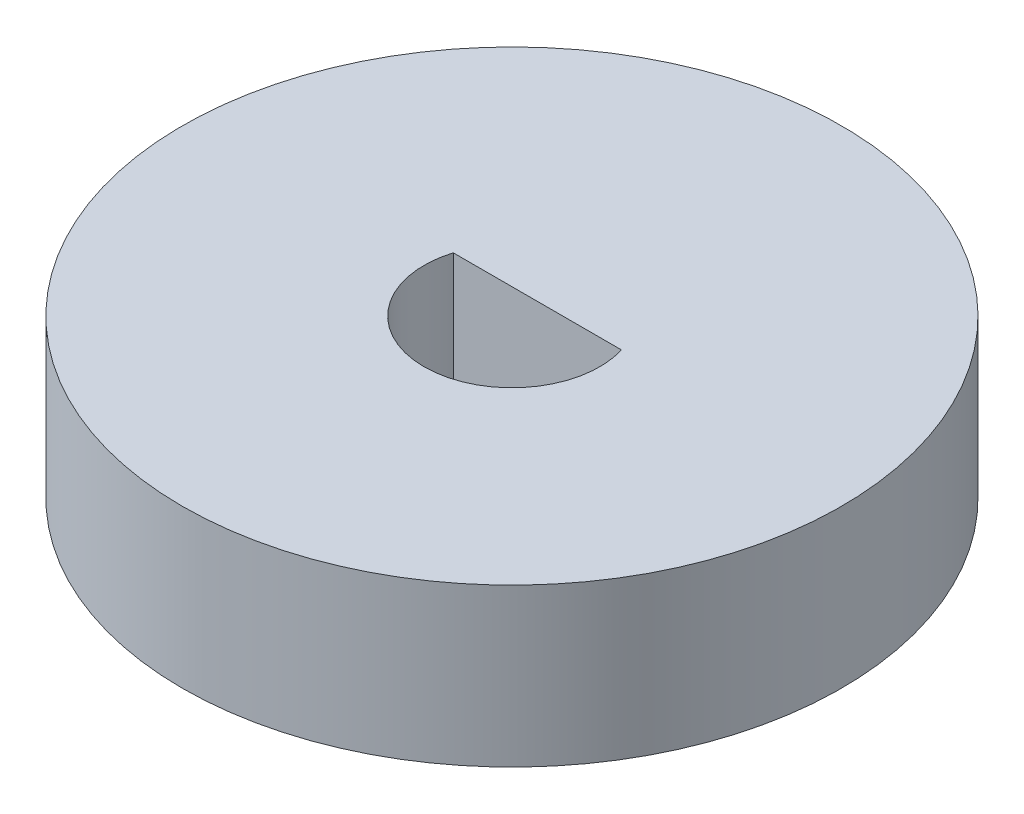
SolidWorks part; units mm, degrees
ref_plane "Front Plane" through (0, 0, 0) normal (0, 0, 1) x (1, 0, 0)
ref_plane "Top Plane" through (0, 0, 0) normal (0, 1, 0) x (1, 0, 0)
ref_plane "Right Plane" through (0, 0, 0) normal (1, 0, 0) x (0, 0, -1)
sketch "Sketch1" plane through (0, 0, 0) normal (0, 1, 0) x (1, 0, 0)
  circle A0 centre (0, 0) radius 11.25
  dimension "D1" = 22.5
extrude "Boss-Extrude1" add sketch "Sketch1" along normal blind 5.38
sketch "Sketch2" plane through (0, 5.38, 0) normal (0, 1, 0) x (1, 0, 0)
  circle A0 centre (0, 0) radius 3
  dimension "D1" = 6
extrude "Cut-Extrude1" cut sketch "Sketch2" against normal blind 5.38
sketch "Sketch3" plane through (0, 5.38, 0) normal (0, 1, 0) x (1, 0, 0)
  line L1 (-3, 3) -> (2.8715, 3)
  line L2 (-3, 3) -> (-3, 0.8685)
  line L3 (-3, 0.8685) -> (2.8715, 0.8685)
  line L4 (2.8715, 3) -> (2.8715, 0.8685)
  circle A0 centre (0, 0) radius 3 construction
extrude "Boss-Extrude2" add sketch "Sketch3" against normal blind 5.38
equation "\"AcrThickness\"= 5.38mm"
equation "\"D1@Boss-Extrude1\"=\"AcrThickness\""
equation "\"D1@Cut-Extrude1\"=\"AcrThickness\""
equation "\"D1@Boss-Extrude2\"=\"AcrThickness\""
